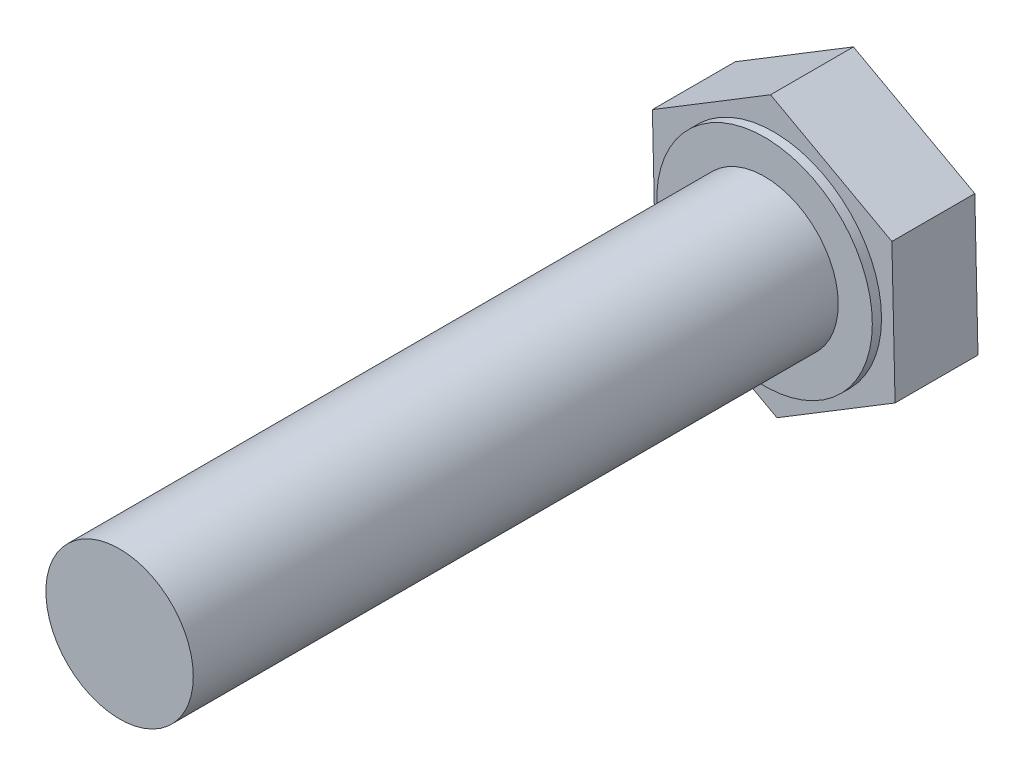
SolidWorks part; units mm, degrees
ref_plane "Front Plane" through (0, 0, 0) normal (0, 0, 1) x (1, 0, 0)
ref_plane "Top Plane" through (0, 0, 0) normal (0, 1, 0) x (1, 0, 0)
ref_plane "Right Plane" through (0, 0, 0) normal (1, 0, 0) x (0, 0, -1)
sketch "Sketch1" plane through (0, 0, 0) normal (0, 0, 1) x (1, 0, 0)
  line L1 (-6.4115, -3.902) -> (0.1734, -7.5035)
  line L2 (0.1734, -7.5035) -> (6.585, -3.6016)
  line L3 (6.585, -3.6016) -> (6.4115, 3.902)
  line L4 (6.4115, 3.902) -> (-0.1734, 7.5035)
  line L5 (-0.1734, 7.5035) -> (-6.585, 3.6016)
  line L6 (-6.585, 3.6016) -> (-6.4115, -3.902)
  circle A0 centre (0, 0) radius 6.5 construction
  dimension "D1" = 13
extrude "Boss-Extrude1" add sketch "Sketch1" along normal blind 4.5
sketch "Sketch2" plane through (0, 0, 4.5) normal (0, 0, 1) x (1, 0, 0)
  circle A0 centre (0, 0) radius 5.85
  dimension "D1" = 11.7
extrude "Boss-Extrude2" add sketch "Sketch2" along normal blind 0.5
sketch "Sketch3" plane through (0, 0, 5) normal (0, 0, 1) x (1, 0, 0)
  circle A0 centre (0, 0) radius 4
  dimension "D1" = 8
extrude "Boss-Extrude3" add sketch "Sketch3" along normal blind 35
cosmetic thread "Cosmetic Thread1" parameters "D1"=28, "D2"=6.619
